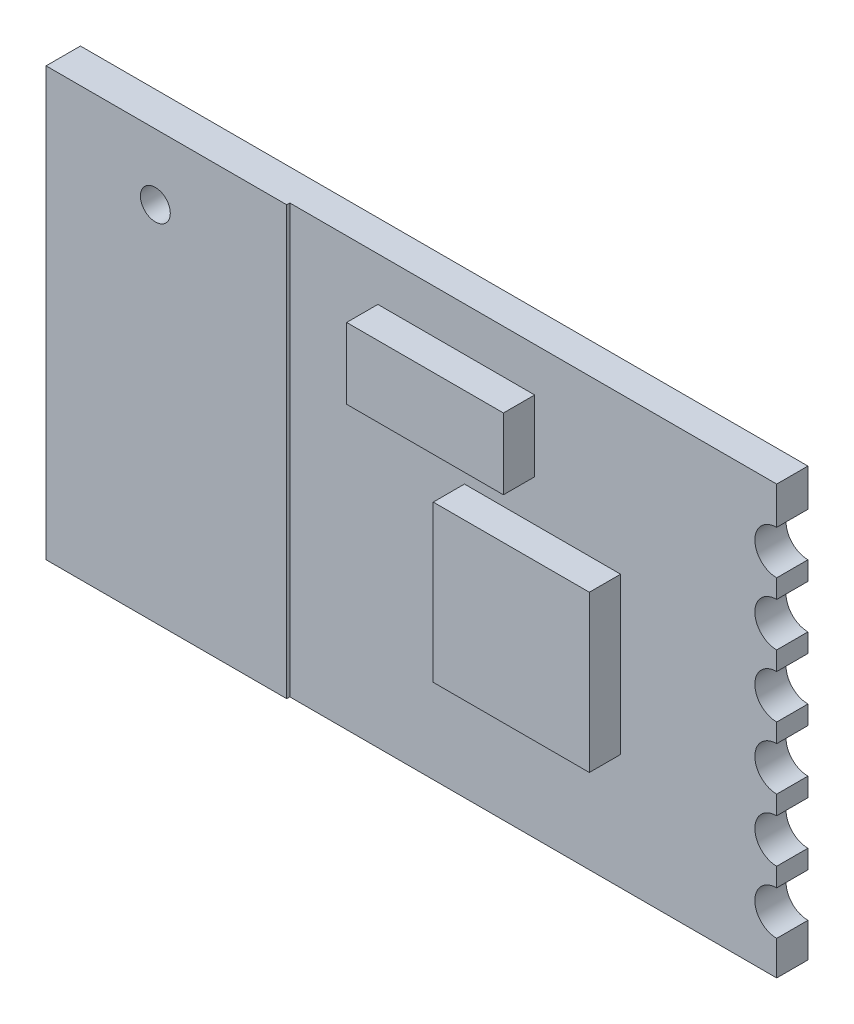
SolidWorks part; units mm, degrees
ref_plane "Front Plane" through (0, 0, 0) normal (0, 0, 1) x (1, 0, 0)
ref_plane "Top Plane" through (0, 0, 0) normal (0, 1, 0) x (1, 0, 0)
ref_plane "Right Plane" through (0, 0, 0) normal (1, 0, 0) x (0, 0, -1)
sketch "Sketch1" plane through (0, 0, 0) normal (0, 0, 1) x (1, 0, 0)
  line L0 (13.8178, 5.3067) -> (13.8178, 4.7067)
  line L1 (-9.4822, 7.9067) -> (13.8178, 7.9067)
  line L2 (-9.4822, 7.9067) -> (-9.4822, -5.7933)
  line L3 (-9.4822, -5.7933) -> (13.8178, -5.7933)
  line L4 (13.8178, 7.9067) -> (13.8178, 6.7067)
  line L5 (13.8178, 3.3067) -> (13.8178, 2.7067)
  line L6 (13.8178, 1.3067) -> (13.8178, 0.7067)
  line L7 (13.8178, -0.6933) -> (13.8178, -1.2933)
  line L8 (13.8178, -2.6933) -> (13.8178, -3.2933)
  line L9 (13.8178, -4.6933) -> (13.8178, -5.7933)
  arc A0 (13.8178, 6.7067) -> (13.8178, 5.3067) centre (13.8178, 6.0067) ccw
  arc A1 (13.8178, 4.7067) -> (13.8178, 3.3067) centre (13.8178, 4.0067) ccw
  arc A2 (13.8178, 2.7067) -> (13.8178, 1.3067) centre (13.8178, 2.0067) ccw
  arc A3 (13.8178, 0.7067) -> (13.8178, -0.6933) centre (13.8178, 0.0067) ccw
  arc A4 (13.8178, -1.2933) -> (13.8178, -2.6933) centre (13.8178, -1.9933) ccw
  arc A5 (13.8178, -3.2933) -> (13.8178, -4.6933) centre (13.8178, -3.9933) ccw
  point P8 (13.598, 3.387)
  point P17 (13.8178, 6.5624)
  point P18 (0, 0)
  point P19 (13.8178, 2.5878)
  point P20 (13.8178, -1.2711)
  point P21 (0, 0)
  point P22 (0, 0)
  point P23 (13.8178, -1.4351)
  point P24 (13.8178, -3.4034)
  dimension "D1" = 23.3
  dimension "D2" = 13.7
  dimension "D3" = 2
  dimension "D4" = 2
  dimension "D5" = 2
  dimension "D6" = 2
  dimension "D7" = 2
  dimension "D8" = 1.9
extrude "Boss-Extrude1" add sketch "Sketch1" along normal blind 1
sketch "Sketch2" plane through (0, 0, 1) normal (0, 0, 1) x (1, 0, 0)
  line L0 (-9.4822, -5.7933) -> (13.8178, -5.7933) construction
  line L1 (-9.4822, 7.9067) -> (-1.7761, 7.9067)
  line L2 (-9.4822, 7.9067) -> (-9.4822, -5.7933)
  line L3 (-9.4822, -5.7933) -> (-1.7761, -5.7933)
  line L4 (-1.7761, 7.9067) -> (-1.7761, -5.7933)
extrude "Boss-Extrude2" add sketch "Sketch2" along normal blind 0.1
sketch "Sketch3" plane through (0, 0, 1.1) normal (0, 0, 1) x (1, 0, 0)
  line L0 (-9.4822, 7.9067) -> (-9.4822, -5.7933) construction
  line L1 (-1.7761, 7.9067) -> (-9.4822, 7.9067) construction
  circle A0 centre (-5.9822, 5.8067) radius 0.4788
  dimension "D1" = 3.5
  dimension "D2" = 2.1
extrude "Cut-Extrude1" cut sketch "Sketch3" against normal blind 2.1
sketch "Sketch4" plane through (0, 0, 1) normal (0, 0, 1) x (1, 0, 0)
  line L0 (13.8178, 7.9067) -> (-1.7761, 7.9067) construction
  line L1 (3.8178, 2.9067) -> (8.8178, 2.9067)
  line L2 (3.8178, 2.9067) -> (3.8178, -2.0933)
  line L3 (3.8178, -2.0933) -> (8.8178, -2.0933)
  line L4 (8.8178, 2.9067) -> (8.8178, -2.0933)
  line L5 (13.8178, -5.7933) -> (13.8178, -4.6933) construction
  point P8 (13.8178, -5.2433)
  dimension "D1" = 5
  dimension "D2" = 5
extrude "Boss-Extrude3" add sketch "Sketch4" along normal blind 1
sketch "Sketch6" plane through (0, 0, 1) normal (0, 0, 1) x (1, 0, 0)
  line L1 (1.0442, 6.5026) -> (6.0659, 6.5026)
  line L2 (1.0442, 6.5026) -> (1.0442, 4.2325)
  line L3 (1.0442, 4.2325) -> (6.0659, 4.2325)
  line L4 (6.0659, 6.5026) -> (6.0659, 4.2325)
extrude "Boss-Extrude5" add sketch "Sketch6" along normal blind 1
